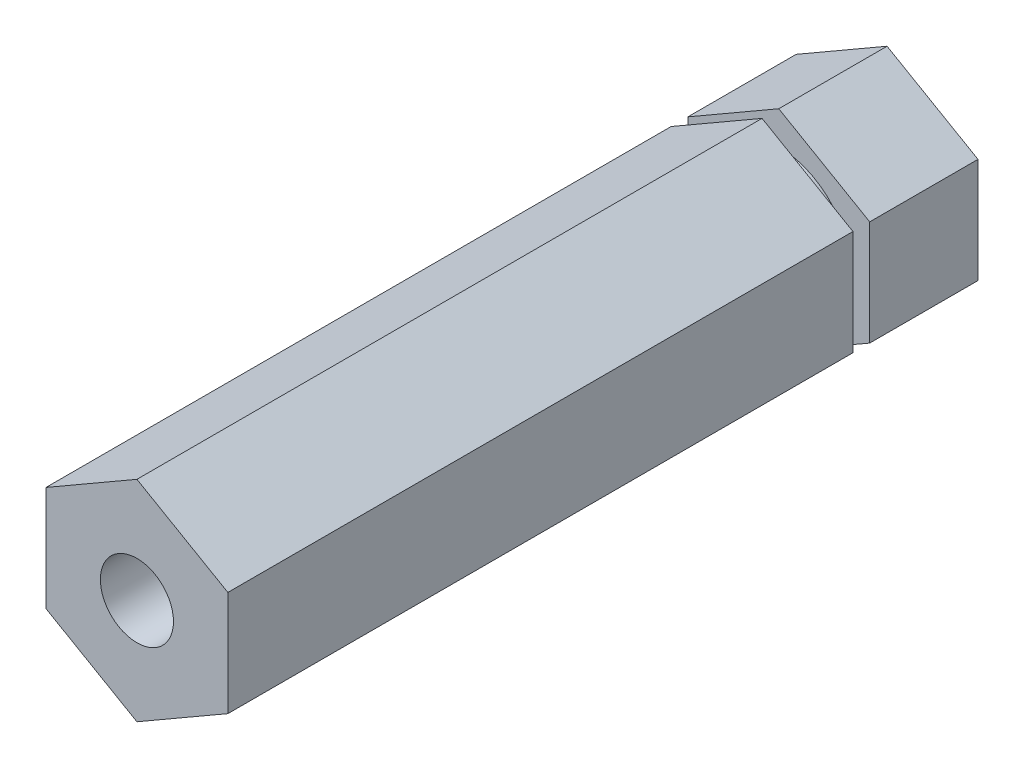
SolidWorks part; units mm, degrees
ref_plane "Front Plane" through (0, 0, 0) normal (0, 0, 1) x (1, 0, 0)
ref_plane "Top Plane" through (0, 0, 0) normal (0, 1, 0) x (1, 0, 0)
ref_plane "Right Plane" through (0, 0, 0) normal (1, 0, 0) x (0, 0, -1)
sketch "Sketch1" plane through (0, 0, 0) normal (0, 0, 1) x (1, 0, 0)
  line L1 (-6.35, 3.6662) -> (-6.35, -3.6662)
  line L2 (-6.35, -3.6662) -> (0, -7.3323)
  line L3 (0, -7.3323) -> (6.35, -3.6662)
  line L4 (6.35, -3.6662) -> (6.35, 3.6662)
  line L5 (6.35, 3.6662) -> (0, 7.3323)
  line L6 (0, 7.3323) -> (-6.35, 3.6662)
  circle A0 centre (0, 0) radius 6.35 construction
  dimension "D1" = 12.7
extrude "Boss-Extrude1" add sketch "Sketch1" along normal mid plane 52.3875
hole_wizard "1/4-20 Tapped Hole1" positions "Sketch2" profile "Sketch4" tap size "1/4-20" standard "ANSI Inch"
sketch "Sketch2" plane through (0, 0, 26.1937) normal (0, 0, 1) x (1, 0, 0)
  point P0 (0, 0)
sketch "Sketch4" plane through (0, 0, 26.1937) normal (1, 0, 0) x (0, -1, 0)
  line L0 (0, 0) -> (0, 20.5838)
  line L1 (0, 20.5838) -> (2.5527, 19.05)
  line L2 (2.5527, 19.05) -> (2.5527, 0)
  line L5 (2.5527, 0) -> (0, 0)
  line L10 (0, 20.5838) -> (-2.5527, 19.05) construction
  line L11 (0, -6.35) -> (0, 107.95) construction
  dimension "Tap Drill Dia." = 5.1054
  dimension "Tap Drill Depth" = 19.05
  dimension "Drill Angle" = 118
cosmetic thread "Hole Thread1" parameters "D1"=12.7, "D2"=6.35
sketch "Sketch5" plane through (0, 0, 0) normal (1, 0, 0) x (0, 0, -1)
  line L0 (26.1937, 0) -> (-26.1937, 0) construction
  line L1 (-26.1937, -3.6662) -> (-26.1937, 3.6662) construction
  line L2 (17.4625, 9.8723) -> (18.6309, 9.8723)
  line L3 (17.4625, 9.8723) -> (17.4625, 5.0292)
  line L4 (17.4625, 5.0292) -> (18.6309, 5.0292)
  line L5 (18.6309, 9.8723) -> (18.6309, 5.0292)
  line L6 (-26.1937, 7.3323) -> (26.1937, 7.3323) construction
  point P4 (0, 0)
  point P9 (18.0467, 5.0292)
  point P10 (0, 0)
  point P11 (-25.4, 0)
  point P14 (18.0467, 9.8723)
  dimension "D1" = 43.6562
  dimension "D2" = 1.1684
  dimension "D3" = 5.0292
  dimension "D4" = 2.54
revolve "Cut-Revolve1" cut sketch "Sketch5" angle 360 about L0
